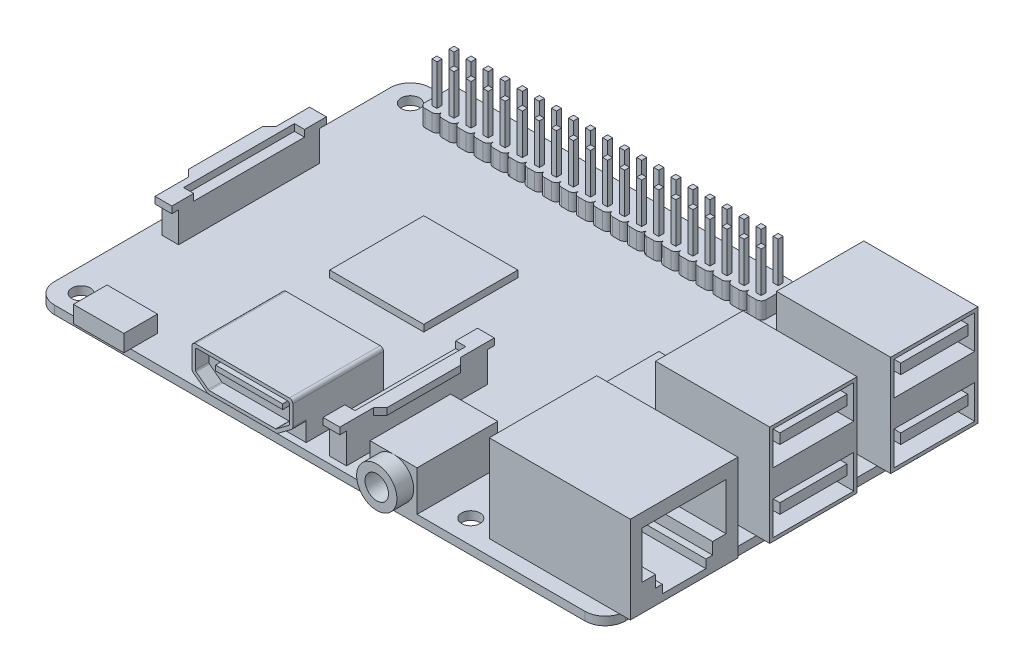
SolidWorks part; units mm, degrees
ref_plane "Front Plane" through (0, 0, 0) normal (0, 0, 1) x (1, 0, 0)
ref_plane "Top Plane" through (0, 0, 0) normal (0, 1, 0) x (1, 0, 0)
ref_plane "Right Plane" through (0, 0, 0) normal (1, 0, 0) x (0, 0, -1)
sketch "Sketch1" plane through (0, 0, 0) normal (0, 1, 0) x (1, 0, 0)
  line L0 (0, 0) -> (0, 49) construction
  line L1 (-0.5, 52.5) -> (78.5, 52.5)
  line L2 (-3.5, 49.5) -> (-3.5, -0.5)
  line L3 (-0.5, -3.5) -> (78.5, -3.5)
  line L4 (81.5, 49.5) -> (81.5, -0.5)
  line L5 (0, 0) -> (58, 0) construction
  line L6 (58, 0) -> (58, 49) construction
  line L7 (0, 49) -> (58, 49) construction
  arc A0 (-0.5, 52.5) -> (-3.5, 49.5) centre (-0.5, 49.5) ccw
  arc A1 (78.5, 52.5) -> (81.5, 49.5) centre (78.5, 49.5) cw
  arc A2 (78.5, -3.5) -> (81.5, -0.5) centre (78.5, -0.5) ccw
  arc A3 (-3.5, -0.5) -> (-0.5, -3.5) centre (-0.5, -0.5) ccw
  circle A4 centre (58, 49) radius 1.375
  circle A5 centre (0, 49) radius 1.375
  circle A6 centre (0, 0) radius 1.375
  circle A7 centre (58, 0) radius 1.375
  dimension "D1" = 56
  dimension "D2" = 85
  dimension "D3" = 58
  dimension "D4" = 49
  dimension "D7" = 2.75
  dimension "D8" = 3
  dimension "D5" = 3.5
  dimension "D6" = 3.5
extrude "Boss-Extrude1" add sketch "Sketch1" along normal blind 1.25
sketch "Sketch2" plane through (0, 1.25, 0) normal (0, -1, 0) x (1, 0, 0)
  line L1 (30.5, -34.5) -> (16.5, -34.5)
  line L2 (30.5, -34.5) -> (30.5, -20.5)
  line L3 (30.5, -20.5) -> (16.5, -20.5)
  line L4 (16.5, -34.5) -> (16.5, -20.5)
  line L5 (60.5, -34.5) -> (51.5, -34.5)
  line L6 (60.5, -34.5) -> (60.5, -25.5)
  line L7 (60.5, -25.5) -> (51.5, -25.5)
  line L8 (51.5, -34.5) -> (51.5, -25.5)
  line L12 (-3.5, -49.5) -> (-3.5, 0.5) construction
  line L13 (-0.5, 3.5) -> (78.5, 3.5) construction
  dimension "D1" = 14
  dimension "D2" = 9
  dimension "D3" = 24
  dimension "D4" = 20
  dimension "D5" = 55
  dimension "D6" = 29
sketch "Sketch4" plane through (0, 1.25, 0) normal (0, 1, 0) x (1, 0, 0)
  line L0 (83.5, 32) -> (83.5, 37) construction
  line L1 (66.5, 50) -> (83.5, 50)
  line L2 (66.5, 50) -> (66.5, 37)
  line L3 (66.5, 37) -> (83.5, 37)
  line L4 (83.5, 50) -> (83.5, 37)
  line L5 (66.5, 32) -> (83.5, 32)
  line L6 (66.5, 32) -> (66.5, 19)
  line L7 (66.5, 19) -> (83.5, 19)
  line L8 (83.5, 32) -> (83.5, 19)
  line L10 (81.5, -0.5) -> (81.5, 49.5) construction
  line L11 (-0.5, -3.5) -> (78.5, -3.5) construction
  point P8 (83.5, 43.5)
  point P13 (83.5, 25.5)
  dimension "D1" = 47
  dimension "D2" = 2
  dimension "D3" = 29
  dimension "D4" = 13
  dimension "D5" = 17
extrude "Boss-Extrude6" add sketch "Sketch4" along normal blind 15
sketch "Sketch21" plane through (83.5, 0, 0) normal (1, 0, 0) x (0, 0, -1)
  line L0 (19, 16.25) -> (19, 1.25) construction
  line L1 (19.5, 15.75) -> (31.5, 15.75)
  line L2 (19.5, 15.75) -> (19.5, 10.75)
  line L3 (19.5, 10.75) -> (31.5, 10.75)
  line L4 (31.5, 15.75) -> (31.5, 10.75)
  line L5 (20.5, 14.75) -> (30.5, 14.75)
  line L6 (20.5, 14.75) -> (20.5, 13.25)
  line L7 (20.5, 13.25) -> (30.5, 13.25)
  line L8 (30.5, 14.75) -> (30.5, 13.25)
  line L9 (19, 8.75) -> (50, 8.75) construction
  line L10 (50, 16.25) -> (50, 1.25) construction
  line L11 (32, 1.25) -> (37, 1.25) construction
  line L12 (32, 16.25) -> (37, 16.25) construction
  line L13 (34.5, 16.25) -> (34.5, 1.25) construction
  line L14 (19.5, 6.75) -> (31.5, 6.75)
  line L15 (19.5, 6.75) -> (19.5, 1.75)
  line L16 (19.5, 1.75) -> (31.5, 1.75)
  line L17 (19, 16.25) -> (32, 16.25) construction
  line L18 (31.5, 6.75) -> (31.5, 1.75)
  line L19 (20.5, 5.75) -> (30.5, 5.75)
  line L20 (32, 16.25) -> (32, 1.25) construction
  line L21 (20.5, 5.75) -> (20.5, 4.25)
  line L22 (20.5, 4.25) -> (30.5, 4.25)
  line L23 (30.5, 5.75) -> (30.5, 4.25)
  line L24 (19, 1.25) -> (32, 1.25) construction
  line L25 (38.5, 5.75) -> (38.5, 4.25)
  line L26 (48.5, 4.25) -> (38.5, 4.25)
  line L27 (48.5, 5.75) -> (48.5, 4.25)
  line L28 (48.5, 5.75) -> (38.5, 5.75)
  line L29 (37.5, 6.75) -> (37.5, 1.75)
  line L30 (49.5, 1.75) -> (37.5, 1.75)
  line L31 (49.5, 6.75) -> (49.5, 1.75)
  line L32 (49.5, 6.75) -> (37.5, 6.75)
  line L33 (38.5, 14.75) -> (38.5, 13.25)
  line L34 (48.5, 13.25) -> (38.5, 13.25)
  line L35 (48.5, 14.75) -> (48.5, 13.25)
  line L36 (48.5, 14.75) -> (38.5, 14.75)
  line L37 (37.5, 15.75) -> (37.5, 10.75)
  line L38 (49.5, 10.75) -> (37.5, 10.75)
  line L39 (49.5, 15.75) -> (49.5, 10.75)
  line L40 (49.5, 15.75) -> (37.5, 15.75)
  dimension "D1" = 0.5
  dimension "D2" = 0.5
  dimension "D3" = 1.5
  dimension "D4" = 0.5
  dimension "D5" = 5
  dimension "D6" = 1
  dimension "D7" = 1
  dimension "D8" = 1
  dimension "D9" = 0.5
  dimension "D10" = 0.5
  dimension "D11" = 0.5
  dimension "D12" = 1
  dimension "D13" = 1
  dimension "D14" = 1
extrude "Cut-Extrude7" cut sketch "Sketch21" against normal offset from surface (13 mm away) 4 up to face at (66.5, 8.75, -25.5)
extrude "Boss-Extrude5" add sketch "Sketch2" against normal blind 1
sketch "Sketch5" plane through (0, 1.25, 0) normal (0, 1, 0) x (1, 0, 0)
  line L0 (81.5, -0.5) -> (81.5, 19) construction
  line L1 (62, 14.75) -> (83, 14.75)
  line L2 (62, 14.75) -> (62, -1.25)
  line L3 (62, -1.25) -> (83, -1.25)
  line L4 (83, 14.75) -> (83, -1.25)
  line L6 (-0.5, -3.5) -> (78.5, -3.5) construction
  point P6 (83, 6.75)
  dimension "D1" = 16
  dimension "D2" = 21
  dimension "D3" = 1.5
  dimension "D4" = 10.25
extrude "Boss-Extrude7" add sketch "Sketch5" along normal blind 13
sketch "Sketch20" plane through (83, 0, 0) normal (1, 0, 0) x (0, 0, -1)
  line L0 (6.75, 14.25) -> (6.75, 1.25) construction
  line L1 (-1.25, 14.25) -> (14.75, 14.25) construction
  line L2 (-1.25, 1.25) -> (14.75, 1.25) construction
  line L3 (13, 12.25) -> (0.5, 12.25)
  line L4 (0.5, 12.25) -> (0.5, 5.25)
  line L5 (0.5, 5.25) -> (2.5, 5.25)
  line L6 (2.5, 5.25) -> (2.5, 3.5)
  line L7 (2.5, 3.5) -> (3.5, 3.5)
  line L8 (3.5, 3.5) -> (3.5, 2.25)
  line L9 (3.5, 2.25) -> (10, 2.25)
  line L10 (10, 3.5) -> (10, 2.25)
  line L11 (11, 3.5) -> (10, 3.5)
  line L12 (11, 5.25) -> (11, 3.5)
  line L13 (13, 5.25) -> (11, 5.25)
  line L14 (13, 12.25) -> (13, 5.25)
  point P16 (6.75, 2.25)
  point P21 (6.75, 12.25)
  dimension "D1" = 7
  dimension "D2" = 2
  dimension "D3" = 1.75
  dimension "D4" = 1
  dimension "D5" = 1.25
  dimension "D6" = 6.25
  dimension "D7" = 2
extrude "Cut-Extrude6" cut sketch "Sketch20" against normal offset from surface (13 mm away) 8 up to face at (62, 7.75, -6.75)
sketch "Sketch8" plane through (0, 1.25, 0) normal (0, 1, 0) x (1, 0, 0)
  line L0 (-3.5, 49.5) -> (-3.5, -0.5) construction
  line L1 (4.25, 52) -> (5.29, 52)
  line L2 (3.5, 51.25) -> (3.5, 47.67)
  line L3 (4.25, 46.92) -> (5.29, 46.92)
  line L4 (6.04, 51.25) -> (6.04, 47.67)
  line L5 (78.5, 52.5) -> (-0.5, 52.5) construction
  arc A0 (4.25, 52) -> (3.5, 51.25) centre (4.25, 51.25) ccw
  arc A1 (5.29, 52) -> (6.04, 51.25) centre (5.29, 51.25) cw
  arc A2 (5.29, 46.92) -> (6.04, 47.67) centre (5.29, 47.67) ccw
  arc A3 (3.5, 47.67) -> (4.25, 46.92) centre (4.25, 47.67) ccw
  point P10 (3.5, 52)
  point P13 (6.04, 52)
  point P18 (3.5, 46.92)
  dimension "D5" = 0.75
  dimension "D6" = 0.75
  dimension "D7" = 0.75
  dimension "D8" = 0.75
  dimension "D1" = 2.54
  dimension "D2" = 5.08
  dimension "D3" = 7
  dimension "D4" = 0.5
extrude "Boss-Extrude9" add sketch "Sketch8" along normal blind 2.5
sketch "Sketch9" plane through (0, 3.75, 0) normal (0, 1, 0) x (1, 0, 0)
  line L0 (4.77, 52) -> (4.77, 46.92) construction
  line L1 (5.29, 52) -> (4.25, 52) construction
  line L2 (4.25, 46.92) -> (5.29, 46.92) construction
  line L3 (5.29, 52) -> (4.25, 52) construction
  line L4 (4.395, 51.105) -> (5.145, 51.105)
  line L5 (4.395, 51.105) -> (4.395, 50.355)
  line L6 (4.395, 50.355) -> (5.145, 50.355)
  line L7 (5.145, 51.105) -> (5.145, 50.355)
  line L8 (4.395, 48.565) -> (5.145, 48.565)
  line L9 (4.395, 48.565) -> (4.395, 47.815)
  line L10 (4.395, 47.815) -> (5.145, 47.815)
  line L11 (5.145, 48.565) -> (5.145, 47.815)
  point P14 (4.77, 51.105)
  point P15 (4.77, 48.565)
  dimension "D1" = 0.75
  dimension "D2" = 1.79
  dimension "D3" = 0.895
extrude "Boss-Extrude10" add sketch "Sketch9" along normal blind 6
pattern_linear "LPattern1" count 20 spacing 2.54 along (1, 0, 0) of "Boss-Extrude10", "Boss-Extrude9"
sketch "Sketch10" plane through (0, 1.25, 0) normal (0, 1, 0) x (1, 0, 0)
  line L0 (-3.5, 49.5) -> (-3.5, -0.5) construction
  line L1 (-1.5, 34.5) -> (1, 34.5)
  line L2 (-1.5, 34.5) -> (-1.5, 13.5)
  line L3 (-1.5, 13.5) -> (1, 13.5)
  line L4 (1, 34.5) -> (1, 13.5)
  line L5 (39.5, 18.5) -> (42, 18.5)
  line L6 (39.5, 18.5) -> (39.5, -2.5)
  line L7 (39.5, -2.5) -> (42, -2.5)
  line L8 (42, 18.5) -> (42, -2.5)
  line L9 (78.5, 52.5) -> (-0.5, 52.5) construction
  line L10 (-0.5, -3.5) -> (78.5, -3.5) construction
  dimension "D1" = 2.5
  dimension "D2" = 21
  dimension "D3" = 2
  dimension "D4" = 18
  dimension "D5" = 43
  dimension "D6" = 1
extrude "Boss-Extrude11" add sketch "Sketch10" along normal blind 4.5
sketch "Sketch11" plane through (0, 5.75, 0) normal (0, 1, 0) x (1, 0, 0)
  line L0 (1, 35.5) -> (-1.5, 35.5)
  line L1 (-1.5, 35.5) -> (-1.5, 30.5)
  line L2 (-1.5, 30.5) -> (-2.5, 29.5)
  line L3 (-2.5, 29.5) -> (-2.5, 18.5)
  line L4 (-2.5, 18.5) -> (-1.5, 17.5)
  line L5 (-1.5, 17.5) -> (-1.5, 12.5)
  line L6 (-1.5, 12.5) -> (1, 12.5)
  line L7 (1, 12.5) -> (1, 15.75)
  line L8 (1, 15.75) -> (-0.5, 15.75)
  line L9 (-0.5, 15.75) -> (-0.5, 32.25)
  line L10 (-0.5, 32.25) -> (1, 32.25)
  line L11 (1, 32.25) -> (1, 35.5)
  line L12 (1, 32.25) -> (1, 15.75) construction
  line L13 (39.5, 19.5) -> (39.5, 16.25)
  line L14 (39.5, 16.25) -> (41, 16.25)
  line L15 (41, 16.25) -> (41, -0.25)
  line L16 (41, -0.25) -> (39.5, -0.25)
  line L17 (1, 13.5) -> (1, 34.5) construction
  line L18 (-1.5, 34.5) -> (-1.5, 13.5) construction
  line L19 (-1.5, 34.5) -> (-1.5, 13.5) construction
  line L20 (1, 34.5) -> (-1.5, 34.5) construction
  line L21 (39.5, -0.25) -> (39.5, -3.5)
  line L22 (39.5, -3.5) -> (42, -3.5)
  line L23 (42, -3.5) -> (42, 1.5)
  line L24 (42, 1.5) -> (43, 2.5)
  line L25 (43, 2.5) -> (43, 13.5)
  line L26 (43, 13.5) -> (42, 14.5)
  line L27 (42, 14.5) -> (42, 19.5)
  line L28 (42, 19.5) -> (39.5, 19.5)
  line L30 (42, -2.5) -> (42, 18.5) construction
  line L31 (39.5, 18.5) -> (39.5, -2.5) construction
  line L32 (42, -2.5) -> (42, 18.5) construction
  line L33 (39.5, 16.25) -> (39.5, -0.25) construction
  line L35 (42, 18.5) -> (39.5, 18.5) construction
  point P17 (1, 24)
  point P18 (1, 24)
  point P41 (39.5, 8)
  point P42 (39.5, 8)
  dimension "D1" = 1
  dimension "D2" = 11
  dimension "D3" = 1
  dimension "D4" = 1
  dimension "D5" = 1
  dimension "D6" = 1.5
  dimension "D7" = 1.5
  dimension "D8" = 11
  dimension "D9" = 16.5
  dimension "D10" = 16.5
  dimension "D11" = 45
  dimension "D12" = 45
extrude "Boss-Extrude12" add sketch "Sketch11" along normal blind 1
sketch "Sketch12" plane through (0, 1.25, 0) normal (0, 1, 0) x (1, 0, 0)
  line L0 (-0.5, -3.5) -> (78.5, -3.5) construction
  line L1 (46.5, 8.5) -> (53.5, 8.5)
  line L2 (46.5, 8.5) -> (46.5, -3.5)
  line L3 (46.5, -3.5) -> (53.5, -3.5)
  line L4 (53.5, 8.5) -> (53.5, -3.5)
  line L6 (-3.5, 49.5) -> (-3.5, -0.5) construction
  point P8 (50, -3.5)
  dimension "D1" = 12
  dimension "D2" = 7
  dimension "D3" = 53.5
extrude "Boss-Extrude13" add sketch "Sketch12" along normal blind 6
sketch "Sketch13" plane through (0, 0, 3.5) normal (0, 0, 1) x (1, 0, 0)
  line L0 (46.5, 7.25) -> (46.5, 1.25) construction
  line L1 (46.5, 7.25) -> (53.5, 7.25) construction
  circle A0 centre (50, 4.25) radius 3
  dimension "D3" = 6
  dimension "D1" = 3.5
  dimension "D2" = 3
extrude "Boss-Extrude14" add sketch "Sketch13" along normal blind 2.5
sketch "Sketch14" plane through (0, 0, 6) normal (0, 0, 1) x (1, 0, 0)
  circle A0 centre (50, 4.25) radius 1.75
  dimension "D1" = 3.5
extrude "Cut-Extrude1" cut sketch "Sketch14" against normal up to next
sketch "Sketch15" plane through (0, 1.25, 0) normal (0, 1, 0) x (1, 0, 0)
  line L0 (-0.5, -3.5) -> (46.5, -3.5) construction
  line L1 (3.35, 0.5) -> (10.85, 0.5)
  line L2 (3.35, 0.5) -> (3.35, -4.5)
  line L3 (3.35, -4.5) -> (10.85, -4.5)
  line L4 (10.85, 0.5) -> (10.85, -4.5)
  line L6 (-3.5, 49.5) -> (-3.5, -0.5) construction
  point P8 (7.1, -4.5)
  dimension "D1" = 7.5
  dimension "D2" = 5
  dimension "D3" = 1
  dimension "D4" = 10.6
extrude "Boss-Extrude15" add sketch "Sketch15" along normal blind 2.5 separate body
sketch "Sketch17" plane through (0, 1.25, 0) normal (0, 1, 0) x (1, 0, 0)
  line L0 (-3.5, 49.5) -> (-3.5, -0.5) construction
  line L1 (21, 9) -> (36, 9)
  line L2 (21, 9) -> (21, -2.5)
  line L3 (21, -2.5) -> (36, -2.5)
  line L4 (36, 9) -> (36, -2.5)
  line L6 (-0.5, -3.5) -> (46.5, -3.5) construction
  point P8 (28.5, -2.5)
  dimension "D1" = 11.5
  dimension "D2" = 15
  dimension "D3" = 1
  dimension "D4" = 32
extrude "Boss-Extrude16" add sketch "Sketch17" along normal blind 6.5
fillet "Fillet1" radius 0.5 2 edges at (21, 7.75, -3.25) (36, 7.75, -3.25)
sketch "Sketch19" plane through (0, 0, 2.5) normal (0, 0, 1) x (1, 0, 0)
  line L0 (21, 4.25) -> (21, 7.25)
  line L1 (21, 7.25) -> (21, 1.25) construction
  line L2 (36, 7.25) -> (36, 1.25) construction
  line L3 (21.6, 4.175) -> (23.4333, 2.8)
  line L4 (23.5, 2.25) -> (33.5, 2.25)
  line L5 (21.2, 3.85) -> (23.2, 2.35)
  line L6 (33.5667, 2.8) -> (35.4, 4.175)
  line L7 (33.8, 2.35) -> (35.8, 3.85)
  line L8 (36, 4.25) -> (36, 7.25)
  line L9 (21.5, 7.75) -> (35.5, 7.75)
  line L11 (21, 1.25) -> (36, 1.25) construction
  line L12 (21.75, 7.25) -> (35.25, 7.25)
  line L13 (35.5, 7) -> (35.5, 4.375)
  line L14 (21.5, 7) -> (21.5, 4.375)
  line L17 (23.5833, 2.75) -> (33.4167, 2.75)
  arc A0 (35.5, 7.75) -> (36, 7.25) centre (35.5, 7.25) cw
  arc A1 (21, 7.25) -> (21.5, 7.75) centre (21.5, 7.25) cw
  arc A2 (23.5833, 2.75) -> (23.4333, 2.8) centre (23.5833, 3) cw
  arc A3 (21.5, 4.375) -> (21.6, 4.175) centre (21.75, 4.375) ccw
  arc A4 (21, 4.25) -> (21.2, 3.85) centre (21.5, 4.25) ccw
  arc A5 (23.5, 2.25) -> (23.2, 2.35) centre (23.5, 2.75) cw
  arc A6 (33.4167, 2.75) -> (33.5667, 2.8) centre (33.4167, 3) ccw
  arc A7 (35.5, 4.375) -> (35.4, 4.175) centre (35.25, 4.375) cw
  arc A8 (21.5, 7) -> (21.75, 7.25) centre (21.75, 7) cw
  arc A9 (35.25, 7.25) -> (35.5, 7) centre (35.25, 7) cw
  arc A10 (33.5, 2.25) -> (33.8, 2.35) centre (33.5, 2.75) ccw
  arc A11 (36, 4.25) -> (35.8, 3.85) centre (35.5, 4.25) cw
  dimension "D1" = 10
  dimension "D2" = 3
  dimension "D3" = 0.5
  dimension "D4" = 1
  dimension "D9" = 0.5
  dimension "D11" = 0.5
  dimension "D12" = 0.25
  dimension "D13" = 0.5
  dimension "D5" = 2.5
  dimension "D6" = 0.5
  dimension "D10" = 0.5
extrude "Boss-Extrude17" add sketch "Sketch19" along normal blind 2
sketch "Sketch22" plane through (0, 0, 0) normal (0, -1, 0) x (1, 0, 0)
  line L0 (-3.5, -49.5) -> (-3.5, 0.5) construction
  line L1 (33.5, -23.5) -> (45.5, -23.5)
  line L2 (33.5, -23.5) -> (33.5, -35.5)
  line L3 (33.5, -35.5) -> (45.5, -35.5)
  line L4 (45.5, -23.5) -> (45.5, -35.5)
  line L5 (-0.5, 3.5) -> (78.5, 3.5) construction
  dimension "D1" = 12
  dimension "D2" = 37
  dimension "D3" = 27
extrude "Boss-Extrude18" add sketch "Sketch22" along normal blind 1
sketch "Sketch23" plane through (0, 0, 2.5) normal (0, 0, 1) x (1, 0, 0)
  line L0 (21, 4.25) -> (21, 1.25) construction
  line L1 (23.5, 5.5) -> (33.5, 5.5)
  line L2 (23.5, 5.5) -> (23.5, 4.75)
  line L3 (23.5, 4.75) -> (33.5, 4.75)
  line L4 (33.5, 5.5) -> (33.5, 4.75)
  line L5 (21, 1.25) -> (36, 1.25) construction
  dimension "D1" = 0.75
  dimension "D2" = 10
  dimension "D3" = 2.5
  dimension "D4" = 3.5
extrude "Boss-Extrude19" add sketch "Sketch23" along normal offset from surface (1 mm away) 1 up to face at (28.5, 4.6259, 4.5)
sketch "Sketch24" plane through (0, 0, 0) normal (0, -1, 0) x (1, 0, 0)
  line L0 (-3.5, -49.5) -> (-3.5, 0.5) construction
  line L1 (-1.5, -18.5) -> (9.5, -18.5)
  line L2 (-1.5, -18.5) -> (-1.5, -30.5)
  line L3 (-1.5, -30.5) -> (9.5, -30.5)
  line L4 (9.5, -18.5) -> (9.5, -30.5)
  line L5 (-0.5, 3.5) -> (78.5, 3.5) construction
  dimension "D1" = 12
  dimension "D2" = 11
  dimension "D3" = 2
  dimension "D4" = 22
extrude "Boss-Extrude20" add sketch "Sketch24" along normal blind 1.25
sketch "Sketch25" plane through (-1.5, 0, 0) normal (-1, 0, 0) x (0, 0, 1)
  line L0 (-18.5, 0) -> (-30.5, 0) construction
  line L1 (-30.25, -0.25) -> (-18.75, -0.25)
  line L2 (-30.25, -0.25) -> (-30.25, -1)
  line L3 (-30.25, -1) -> (-18.75, -1)
  line L4 (-18.75, -0.25) -> (-18.75, -1)
  line L5 (-18.5, -1.25) -> (-30.5, -1.25) construction
  line L6 (-18.5, -1.25) -> (-18.5, 0) construction
  line L7 (-30.5, -1.25) -> (-30.5, 0) construction
  dimension "D1" = 0.25
  dimension "D2" = 0.25
  dimension "D3" = 0.25
  dimension "D4" = 0.25
extrude "Cut-Extrude8" cut sketch "Sketch25" against normal offset from surface (9 mm away) 2 up to face at (9.5, -0.625, -24.5)
sketch "Sketch26" plane through (0, -1.25, 0) normal (0, -1, 0) x (1, 0, 0)
  line L0 (-1.5, -18.5) -> (-1.5, -30.5) construction
  line L1 (-1.5, -20) -> (-0.5, -20)
  line L2 (-1.5, -20) -> (-1.5, -28.5)
  line L3 (-1.5, -28.5) -> (-0.5, -28.5)
  line L4 (-0.25, -20.25) -> (-0.25, -28.25)
  line L5 (-1.5, -30.5) -> (9.5, -30.5) construction
  arc A0 (-0.5, -28.5) -> (-0.25, -28.25) centre (-0.5, -28.25) ccw
  arc A1 (-0.5, -20) -> (-0.25, -20.25) centre (-0.5, -20.25) cw
  dimension "D1" = 0.25
  dimension "D2" = 8.5
  dimension "D3" = 1.25
  dimension "D4" = 2
extrude "Cut-Extrude9" cut sketch "Sketch26" against normal up to next (0.25 mm away)
equation "\"D3@LPattern1\"=2.54/2"
